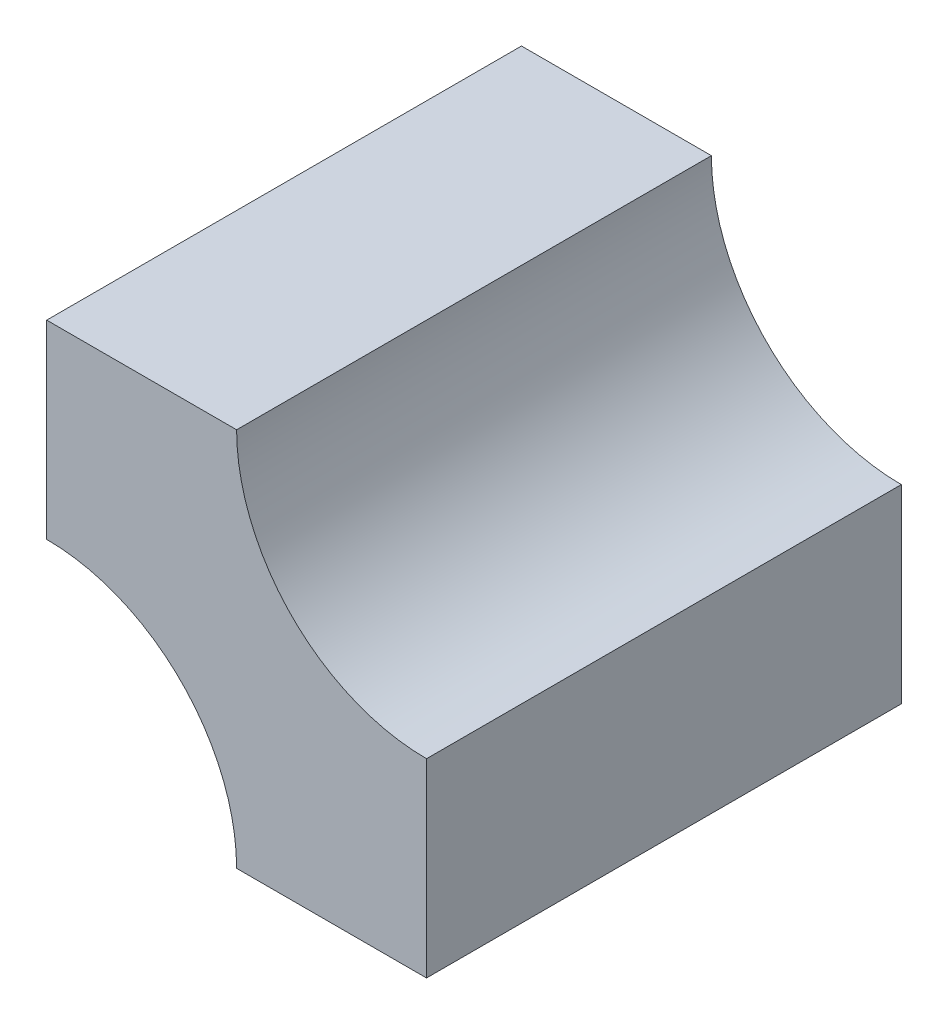
SolidWorks part; units mm, degrees
ref_plane "Front Plane" through (0, 0, 0) normal (0, 0, 1) x (1, 0, 0)
ref_plane "Top Plane" through (0, 0, 0) normal (0, 1, 0) x (1, 0, 0)
ref_plane "Right Plane" through (0, 0, 0) normal (1, 0, 0) x (0, 0, -1)
sketch "Sketch1" plane through (0, 0, 0) normal (0, 0, 1) x (1, 0, 0)
  line L0 (-20, 10) -> (-20, 20)
  line L1 (-20, 20) -> (-10, 20)
  line L2 (0, 10) -> (0, 0)
  line L3 (0, 0) -> (-10, 0)
  arc A0 (-10, 20) -> (0, 10) centre (0, 20) ccw
  arc A1 (-10, 0) -> (-20, 10) centre (-20, 0) ccw
  dimension "D4" = 10
  dimension "D1" = 10
  dimension "D2" = 10
  dimension "D3" = 10
extrude "Boss-Extrude1" add sketch "Sketch1" along normal blind 25
